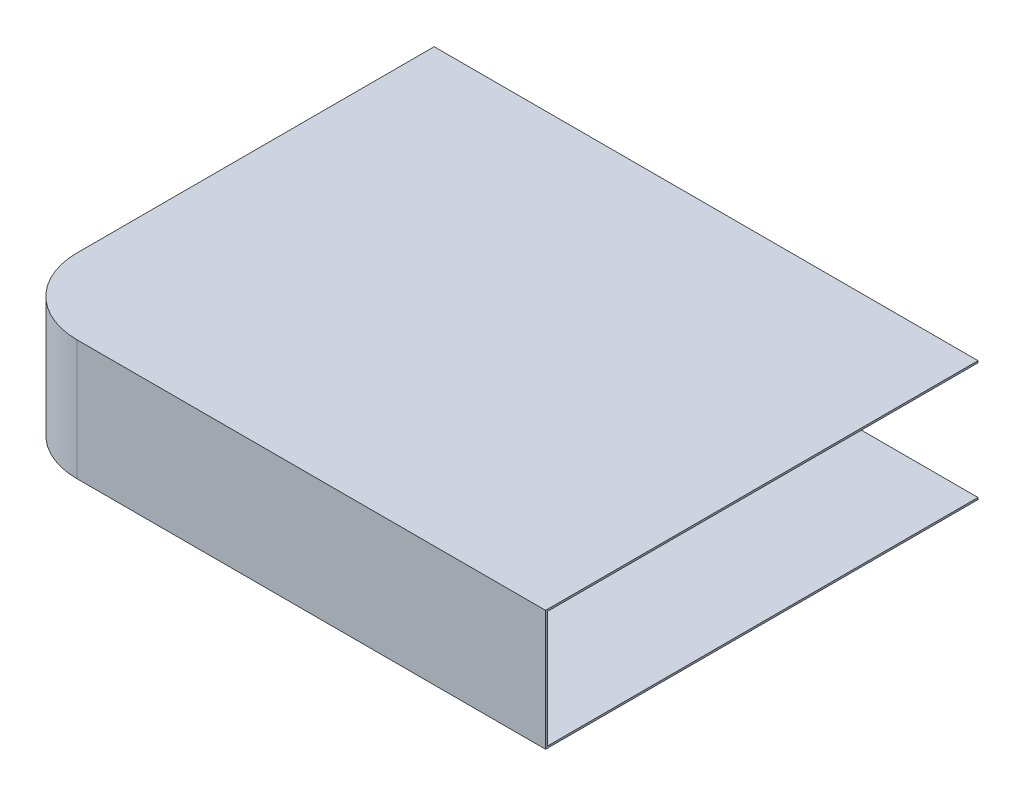
SolidWorks part; units mm, degrees
ref_plane "Alzado" through (0, 0, 0) normal (0, 0, 1) x (1, 0, 0)
ref_plane "Planta" through (0, 0, 0) normal (0, 1, 0) x (1, 0, 0)
ref_plane "Vista lateral" through (0, 0, 0) normal (1, 0, 0) x (0, 0, -1)
sketch "Croquis1" plane through (0, 0, 0) normal (0, 1, 0) x (1, 0, 0)
  line L1 (20, 0) -> (144.6079, 0)
  line L2 (0, 20) -> (0, 117.9862)
  line L3 (0, 117.9862) -> (144.6079, 117.9862)
  line L4 (144.6079, 0) -> (144.6079, 117.9862)
  arc A0 (20, 0) -> (0, 20) centre (20, 20) cw
  point P7 (0, 0)
  dimension "D1" = 20
extrude "Saliente-Extruir1" add sketch "Croquis1" along normal blind 32
shell "Vaciado1" thickness 0.5
sketch "Croquis3" plane through (0, 0, 0) normal (0, 0, 1) x (1, 0, 0)
  line L1 (144.6079, 31.5) -> (0, 31.5)
  line L2 (144.6079, 31.5) -> (144.6079, 0)
  line L3 (144.6079, 0) -> (0, 0)
  line L4 (0, 31.5) -> (0, 0)
  point P4 (0, 0)
sketch "Croquis4" plane through (0, 0, -117.9862) normal (0, 0, -1) x (-1, 0, 0)
  line L1 (-144.6079, 0) -> (0, 0)
  line L2 (-144.6079, 0) -> (-144.6079, 32)
  line L3 (-144.6079, 32) -> (0, 32)
  line L4 (0, 0) -> (0, 32)
extrude "Cortar-Extruir2" cut sketch "Croquis4" against normal blind 3
